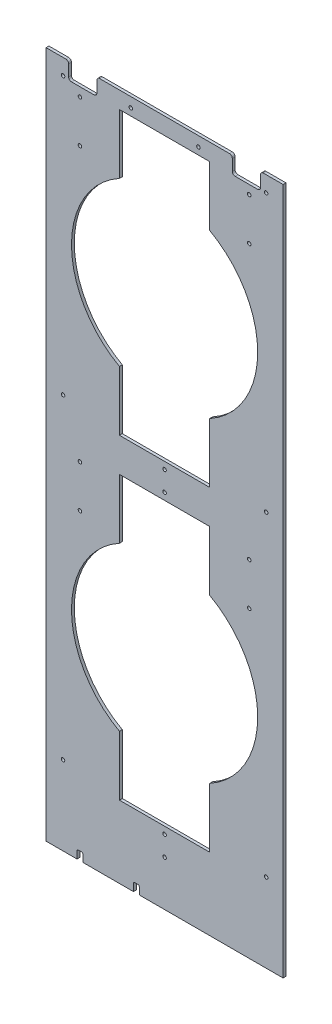
SolidWorks part; units mm, degrees
material "PC High Viscosity"
ref_plane "Front Plane" through (0, 0, 0) normal (0, 0, 1) x (1, 0, 0)
ref_plane "Top Plane" through (0, 0, 0) normal (0, 1, 0) x (1, 0, 0)
ref_plane "Right Plane" through (0, 0, 0) normal (1, 0, 0) x (0, 0, -1)
sketch "Sketch1" plane through (0, 0, 0) normal (0, 0, 1) x (1, 0, 0)
  line L0 (-101.6, 797.56) -> (101.6, 797.56)
  line L1 (-266.7, 0) -> (266.7, 0)
  line L2 (-266.7, 0) -> (-266.7, 2413)
  line L3 (-266.7, 2413) -> (266.7, 2413)
  line L4 (266.7, 0) -> (266.7, 2413)
  line L5 (-101.6, 162.56) -> (101.6, 162.56)
  line L6 (-209.55, 480.06) -> (209.55, 480.06) construction
  line L7 (-101.6, 162.56) -> (-101.6, 296.788)
  line L8 (101.6, 162.56) -> (101.6, 296.788)
  line L9 (101.6, 797.56) -> (101.6, 663.332)
  line L10 (-101.6, 797.56) -> (-101.6, 663.332)
  line L11 (-101.6, 1508.76) -> (-101.6, 1374.532)
  line L12 (-101.6, 873.76) -> (-101.6, 1007.988)
  line L13 (-101.6, 873.76) -> (101.6, 873.76)
  line L14 (101.6, 873.76) -> (101.6, 1007.988)
  line L15 (101.6, 1508.76) -> (101.6, 1374.532)
  line L16 (-101.6, 1508.76) -> (101.6, 1508.76)
  line L17 (-101.6, 2219.96) -> (-101.6, 2085.732)
  line L18 (-101.6, 1584.96) -> (-101.6, 1719.188)
  line L19 (-101.6, 1584.96) -> (101.6, 1584.96)
  line L20 (101.6, 1584.96) -> (101.6, 1719.188)
  line L21 (101.6, 2219.96) -> (101.6, 2085.732)
  line L22 (-101.6, 2219.96) -> (101.6, 2219.96)
  arc A0 (-101.6, 663.332) -> (-101.6, 296.788) centre (0, 480.06) ccw
  arc A1 (101.6, 296.788) -> (101.6, 663.332) centre (0, 480.06) ccw
  arc A2 (-101.6, 1374.532) -> (-101.6, 1007.988) centre (0, 1191.26) ccw
  arc A3 (101.6, 1007.988) -> (101.6, 1374.532) centre (0, 1191.26) ccw
  arc A4 (-101.6, 2085.732) -> (-101.6, 1719.188) centre (0, 1902.46) ccw
  arc A5 (101.6, 1719.188) -> (101.6, 2085.732) centre (0, 1902.46) ccw
  circle A6 centre (0, 480.06) radius 241.3 construction
  point P11 (0, 797.56)
  point P12 (0, 162.56)
  dimension "D3" = 419.1
  dimension "D9" = 482.6
  dimension "D10" = 25.4
  dimension "D1" = 2413
  dimension "D2" = 533.4
  dimension "D4" = 635
  dimension "D5" = 480.06
  dimension "D6" = 203.2
  dimension "D8" = 711.2
  dimension "D11" = 57.15
  dimension "D7" = 3
extrude "Boss-Extrude1" add sketch "Sketch1" along normal blind 6.35
hole_wizard "5/16 (0.3125) Diameter Hole1" positions "Sketch2" profile "Sketch3" hole size "5/16" standard "ANSI Inch" end condition through all
sketch "Sketch2" plane through (0, 0, 6.35) normal (0, 0, 1) x (1, 0, 0)
  line L0 (0, 0) -> (0, 2413) construction
  line L1 (-266.7, 0) -> (266.7, 0) construction
  line L2 (266.7, 2413) -> (-266.7, 2413) construction
  line L4 (0, 146.685) -> (0, 102.235) construction
  line L5 (0, 124.46) -> (-266.7, 124.46) construction
  line L7 (-101.6, 162.56) -> (101.6, 162.56) construction
  line L8 (-266.7, 2413) -> (-266.7, 0) construction
  line L9 (-76.2, 1569.085) -> (-76.2, 1524.635) construction
  line L11 (-76.2, 1546.86) -> (0, 1546.86) construction
  point P0 (0, 146.685)
  point P4 (0, 102.235)
  point P8 (-228.6, 177.8)
  point P43 (0, 857.885)
  point P44 (0, 813.435)
  point P57 (228.6, 177.8)
  point P62 (-228.6, 889)
  point P63 (228.6, 889)
  point P72 (-76.2, 1524.635)
  point P74 (-76.2, 1569.085)
  point P76 (76.2, 1569.085)
  point P78 (76.2, 1524.635)
  point P94 (-228.6, 1511.3)
  point P96 (228.6, 1511.3)
  dimension "D1" = 44.45
  dimension "D2" = 38.1
  dimension "D6" = 177.8
  dimension "D7" = 38.1
  dimension "D3" = 711.2
  dimension "D5" = 76.2
  dimension "D8" = 711.2
  dimension "D9" = 711.2
  dimension "D10" = 1511.3
  dimension "D4" = 2
sketch "Sketch3" plane through (0, 146.685, 6.35) normal (1, 0, 0) x (0, -1, 0)
  line L0 (0, 0) -> (0, 6.35)
  line L1 (0, 6.35) -> (3.9687, 6.35)
  line L2 (3.9687, 6.35) -> (3.9687, 0)
  line L5 (3.9687, 0) -> (0, 0)
  line L11 (0, -6.35) -> (0, 107.95) construction
  dimension "Thru Hole Dia." = 7.9375
  dimension "Thru Hole Depth" = 6.35
sketch "Sketch6" plane through (0, 0, 6.35) normal (0, 0, 1) x (1, 0, 0)
  line L0 (-266.7, 2413) -> (-266.7, 0) construction
  line L1 (-266.7, 1546.86) -> (266.7, 1546.86)
  line L2 (-266.7, 1546.86) -> (-266.7, 2413)
  line L3 (-266.7, 2413) -> (266.7, 2413)
  line L4 (266.7, 1546.86) -> (266.7, 2413)
  line L5 (-76.2, 1569.085) -> (-76.2, 1524.635) construction
  point P8 (-76.2, 1546.86)
extrude "Cut-Extrude1" cut sketch "Sketch6" against normal through all
sketch "Sketch8" plane through (0, 0, 6.35) normal (0, 0, 1) x (1, 0, 0)
  line L0 (-266.7, 1546.86) -> (266.7, 1546.86) construction
  line L1 (-152.4, 1546.86) -> (-215.9, 1546.86)
  line L2 (-152.4, 1546.86) -> (-152.4, 1508.76)
  line L3 (-152.4, 1508.76) -> (-215.9, 1508.76)
  line L4 (-215.9, 1546.86) -> (-215.9, 1508.76)
  line L5 (0, 1546.86) -> (0, 1508.76) construction
  line L6 (101.6, 1508.76) -> (-101.6, 1508.76) construction
  line L7 (152.4, 1508.76) -> (215.9, 1508.76)
  line L8 (215.9, 1546.86) -> (215.9, 1508.76)
  line L9 (152.4, 1546.86) -> (215.9, 1546.86)
  line L10 (152.4, 1546.86) -> (152.4, 1508.76)
  line L11 (-101.6, 1508.76) -> (-101.6, 1374.532) construction
  dimension "D1" = 50.8
  dimension "D2" = 63.5
  dimension "D3" = 38.1
extrude "Cut-Extrude2" cut sketch "Sketch8" against normal through all contours L2 L1 L4 L3 | L7 L8 L9 L10
fillet "Fillet1" radius 6.35 8 edges at (152.4, 1508.76, 3.175) (215.9, 1508.76, 3.175) (215.9, 1546.86, 3.175) (152.4, 1546.86, 3.175) (-152.4, 1546.86, 3.175) (-152.4, 1508.76, 3.175) (-215.9, 1508.76, 3.175) (-215.9, 1546.86, 3.175)
hole_wizard "5/16 (0.3125) Diameter Hole2" positions "Sketch10" profile "Sketch11" hole size "5/16" standard "ANSI Inch" end condition through all
sketch "Sketch10" plane through (0, 0, 6.35) normal (0, 0, 1) x (1, 0, 0)
  line L0 (0, 0) -> (0, 1546.86) construction
  line L1 (-266.7, 0) -> (266.7, 0) construction
  line L2 (-146.05, 1546.86) -> (146.05, 1546.86) construction
  line L4 (-190.5, 682.382) -> (-190.5, 1393.582) construction
  point P0 (-190.5, 682.382)
  point P2 (-190.5, 777.632)
  point P4 (190.5, 777.632)
  point P6 (190.5, 682.382)
  point P29 (-190.5, 1393.582)
  point P30 (-190.5, 1488.832)
  point P31 (190.5, 1488.832)
  point P32 (190.5, 1393.582)
  dimension "D1" = 190.5
  dimension "D2" = 19.05
  dimension "D3" = 95.25
  dimension "D5" = 711.2
  dimension "D4" = 2
sketch "Sketch11" plane through (-190.5, 682.382, 6.35) normal (1, 0, 0) x (0, -1, 0)
  line L0 (0, 0) -> (0, 6.35)
  line L1 (0, 6.35) -> (3.9687, 6.35)
  line L2 (3.9687, 6.35) -> (3.9687, 0)
  line L5 (3.9687, 0) -> (0, 0)
  line L11 (0, -6.35) -> (0, 107.95) construction
  dimension "Thru Hole Dia." = 7.9375
  dimension "Thru Hole Depth" = 6.35
sketch "Sketch12" plane through (0, 0, 6.35) normal (0, 0, 1) x (1, 0, 0)
  line L0 (0, 162.56) -> (0, 0) construction
  line L1 (-101.6, 162.56) -> (101.6, 162.56) construction
  line L2 (-266.7, 0) -> (266.7, 0) construction
  line L4 (-56.896, 0) -> (-70.104, 0)
  line L5 (-56.896, 0) -> (-56.896, 19.05)
  line L6 (-56.896, 19.05) -> (-70.104, 19.05)
  line L7 (-70.104, 0) -> (-70.104, 19.05)
  line L8 (-183.896, 0) -> (-197.104, 0)
  line L9 (-183.896, 0) -> (-183.896, 19.05)
  line L10 (-183.896, 19.05) -> (-197.104, 19.05)
  line L11 (-197.104, 0) -> (-197.104, 19.05)
  point P14 (-63.5, 0)
  point P15 (-190.5, 0)
  dimension "D1" = 63.5
  dimension "D2" = 127
  dimension "D3" = 19.05
  dimension "D4" = 13.208
extrude "Cut-Extrude3" cut sketch "Sketch12" against normal through all
fillet "Fillet2" radius 3.175 4 edges at (-56.896, 19.05, 3.175) (-183.896, 19.05, 3.175) (-70.104, 19.05, 3.175) (-197.104, 19.05, 3.175)
equation "\"D1@Sketch2\"=1.5+.25"
